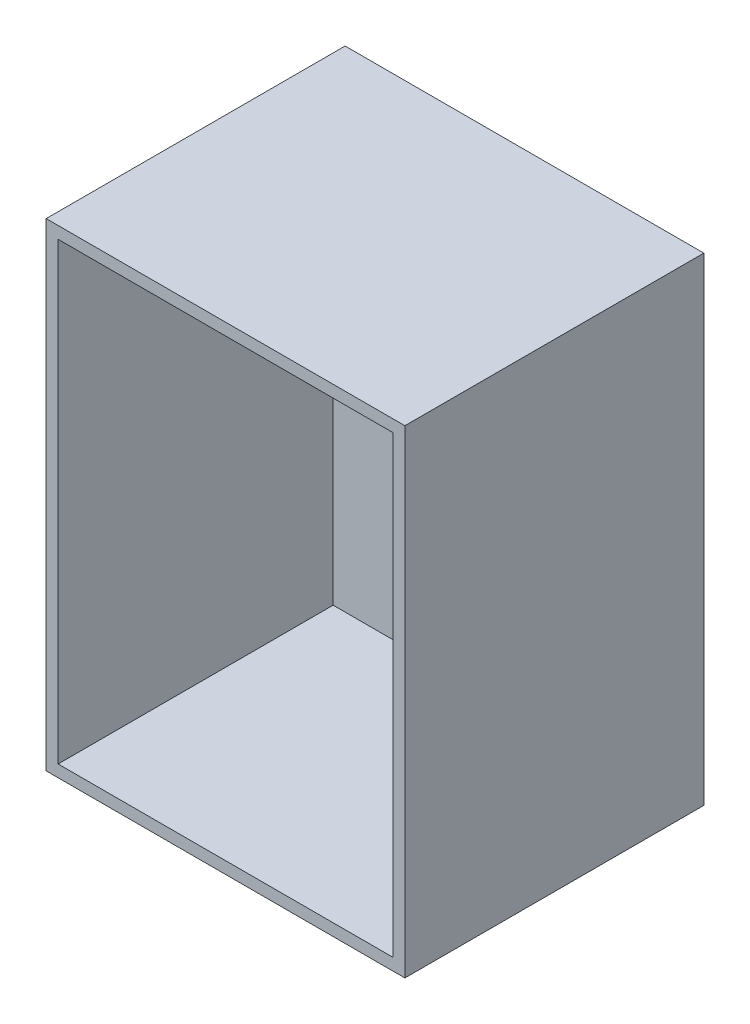
SolidWorks part; units mm, degrees
ref_plane "前视基准面" through (0, 0, 0) normal (0, 0, 1) x (1, 0, 0)
ref_plane "上视基准面" through (0, 0, 0) normal (0, 1, 0) x (1, 0, 0)
ref_plane "右视基准面" through (0, 0, 0) normal (1, 0, 0) x (0, 0, -1)
sketch "草图1" plane through (0, 0, 0) normal (0, 0, 1) x (1, 0, 0)
  line L1 (-17.122, 3.5854) -> (12.878, 3.5854)
  line L2 (-17.122, 3.5854) -> (-17.122, -36.4146)
  line L3 (-17.122, -36.4146) -> (12.878, -36.4146)
  line L4 (12.878, 3.5854) -> (12.878, -36.4146)
  dimension "D1" = 30
  dimension "D2" = 40
extrude "凸台-拉伸1" add sketch "草图1" along normal blind 25
sketch "草图2" plane through (0, 0, 25) normal (0, 0, 1) x (1, 0, 0)
  line L0 (-16.122, 2.5854) -> (-16.122, -35.4146)
  line L1 (-17.122, 3.5854) -> (12.878, 3.5854)
  line L2 (-17.122, 3.5854) -> (-17.122, -36.4146)
  line L3 (-17.122, -36.4146) -> (12.878, -36.4146)
  line L4 (12.878, 3.5854) -> (12.878, -36.4146)
  line L5 (-16.122, -35.4146) -> (11.878, -35.4146)
  line L6 (11.878, 2.5854) -> (11.878, -35.4146)
  line L7 (-16.122, 2.5854) -> (11.878, 2.5854)
  dimension "D1" = 1
extrude "切除-拉伸1" cut sketch "草图2" against normal blind 23 contours L0 L5 L6 L7
